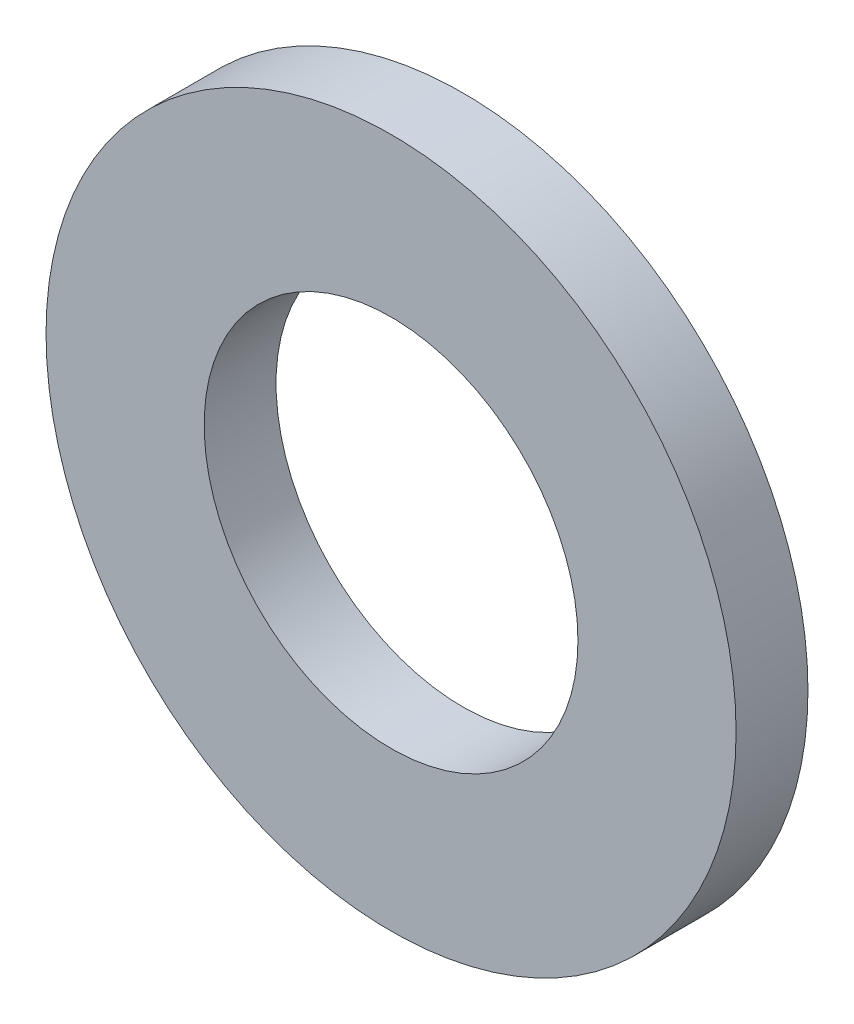
SolidWorks part; units mm, degrees
material "Сталь"
ref_plane "Спереди" through (0, 0, 0) normal (0, 0, 1) x (1, 0, 0)
ref_plane "Сверху" through (0, 0, 0) normal (0, 1, 0) x (1, 0, 0)
ref_plane "Справа" through (0, 0, 0) normal (1, 0, 0) x (0, 0, -1)
sketch "Эскиз1" plane through (0, 0, 0) normal (0, 0, 1) x (1, 0, 0)
  circle A0 centre (0, 0) radius 6.5
  circle A1 centre (0, 0) radius 12
  dimension "D1" = 24
  dimension "D2" = 13
extrude "Бобышка-Вытянуть1" add sketch "Эскиз1" along normal blind 2.5
